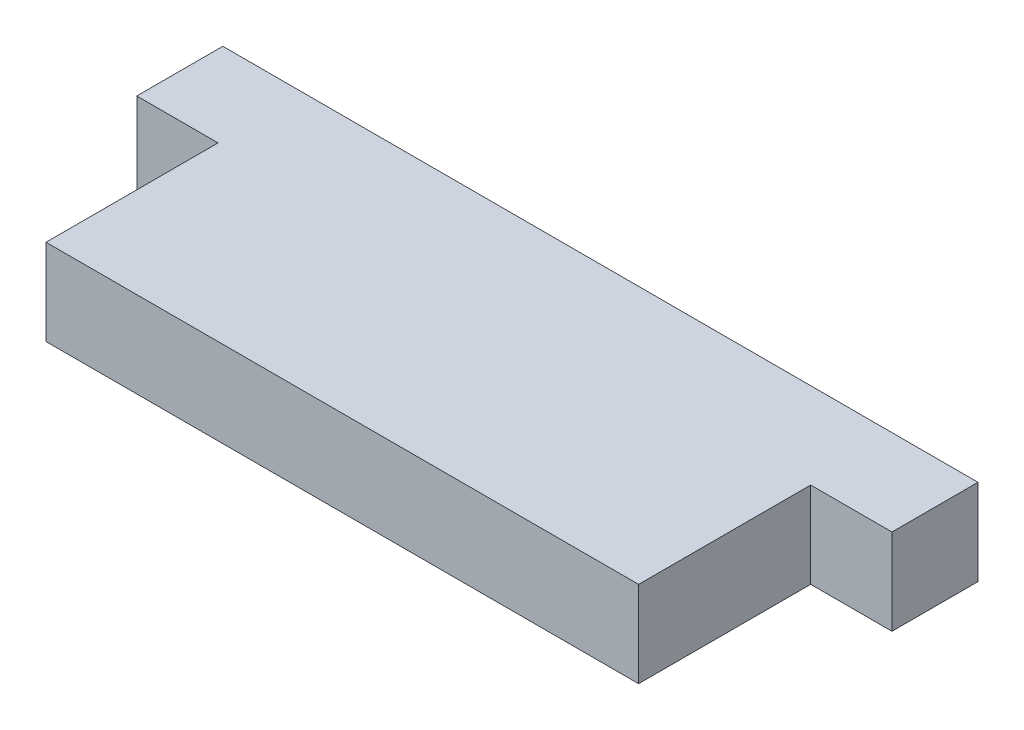
SolidWorks part; units mm, degrees
material "Beech"
ref_plane "Front Plane" through (0, 0, 0) normal (0, 0, 1) x (1, 0, 0)
ref_plane "Top Plane" through (0, 0, 0) normal (0, 1, 0) x (1, 0, 0)
ref_plane "Right Plane" through (0, 0, 0) normal (1, 0, 0) x (0, 0, -1)
sketch "Sketch1" plane through (0, 0, 0) normal (0, 1, 0) x (1, 0, 0)
  line L0 (0, 0) -> (0, 12.7)
  line L1 (0, 0) -> (43.74, 0)
  line L3 (43.74, 0) -> (43.74, 12.7)
  line L4 (-6.0001, 19.05) -> (49.7401, 19.05)
  line L5 (-6.0001, 19.05) -> (-6.0001, 12.7)
  line L6 (49.7401, 19.05) -> (49.7401, 12.7)
  line L7 (-6.0001, 12.7) -> (0, 12.7)
  line L8 (43.74, 12.7) -> (49.7401, 12.7)
  dimension "D1" = 12.7
  dimension "D2" = 43.74
  dimension "D3" = 6.35
  dimension "D4" = 6.0001
  dimension "D5" = 6.0001
extrude "Boss-Extrude1" add sketch "Sketch1" along normal blind 6.35
equation "\"MotorMountLegLength\"=.25in"
equation "\"GearOffset\"=.264907in"
equation "\"D4@Sketch1\"=\"TriggerRackOffset\""
equation "\"D5@Sketch1\"=\"TriggerRackOffset\""
equation "\"D2@Sketch1\" = \"CageLeftBottomEdge\" + \"CageRightBottomEdge\""
equation "\"CageLeftBottomEdge\"=22.11mm"
equation "\"CageLeftTopEdge\"=22.11mm"
equation "\"CageRightBottomEdge\"=21.63mm"
equation "\"CageRightTopEdge\"=21.63mm"
equation "\"CageHeight\"=86.04mm"
equation "\"CageLength\"=73.76mm"
equation "\"CageTopScrewClearance\"=10mm"
equation "\"CageBottomScrewClearance\"=25mm"
equation "\"CageLeftTopDepth\"= 11.65mm"
equation "\"CageLeftBottomDepth\"=11.11mm"
equation "\"CageLeftTopHeight\"=8.56175mm"
equation "\"CageLeftBottomHeight\"=16mm"
equation "\"CageRightTopDepth\"= 11.05mm"
equation "\"CageRightBottomDepth\"=10.58mm"
equation "\"CageRightTopHeight\"=9.6mm"
equation "\"CageRightBottomHeight\"=15.49mm"
equation "\"CageLeftTopChannelDepth\"=2.41908mm"
equation "\"CageLeftBottomChannelDepth\"=2.588mm"
equation "\"CageLeftChannelHeight\"=11.7mm"
equation "\"CageRightTopChannelDepth\"=2.32mm"
equation "\"CageRightBottomChannelDepth\"=2.318mm"
equation "\"CageRightChannelHeight\"=10mm"
equation "\"CageChanRelHeight\"=23.99mm"
equation "\"CageChanRelDepth\"=5.492mm"
equation "\"CageChamberRadius\"=16.261mm"
equation "\"CageScrewDiameter\"=4.8mm"
equation "\"CageSetScrewDiameter\"=3.5mm"
equation "\"CageAxleRadius\"=6.639mm"
equation "\"CageAxleKeyHeight\"=1.619mm"
equation "\"CageAxleKeyWidth\"=2.662mm"
equation "\"CageHoseWindowWidth\"=16.29mm"
equation "\"CageHoseWindowHeight\"=26.5mm"
equation "\"CageHoseWindow-Edge\"=8.89mm"
equation "\"CageScrew-VerticalEdge\"=5.0mm"
equation "\"CageScrew-HorizontalEdge\"=7.5mm"
equation "\"CageScrew-HoseCornerScrewEdge\"=4.45mm"
equation "\"CageAxle-BottomEdge\"=56.05mm"
equation "\"CageAxle-FrontEdge\"=46.03mm"
equation "\"CageBackSetScrew-Axle\"=40mm"
equation "\"CageFrontSetScrew-Axle\"=22mm"
equation "\"CageVelocityWindow-BackEdge\"=34.8mm"
equation "\"CageVelocityWindow-BottomEdge\"=27.55mm"
equation "\"CageVelocityWindowHeight\"=22.29mm"
equation "\"CageVelocityWindowWidth\"=12.61mm"
equation "\"TriggerSlot-BottomEdge\"=6.35mm"
equation "\"TriggerSlot-FrontEdge\"=15mm"
equation "\"TriggerSlotSize\"=6.7mm"
equation "\"TriggerRackOffset\"=.236224in"
equation "\"TriggerSlotSizeInt\"=.25in"
equation "\"TriggerSlotSpacing\"=.25in"
equation "\"TriggerMiniSlotWidth\"=3.5mm"
equation "\"TriggerRackWidth\"=6.5mm"
equation "\"whitemotordepth\"=11.27mm"
equation "\"whitemotorbackdepth\"=3.845mm"
equation "\"whitemotoraxledepth\" = 3.5mm"
equation "\"whitemotoraxleoffset\"=11.4mm"
equation "\"whitemotorwidth\"=12.07mm"
equation "\"whitemotorheight\"=16.68mm"
equation "\"whitemotorcylinderlength\" =13.04mm"
equation "\"whitemotorcylinderradius\"=3.845mm"
equation "\"whitemotorcylinderoffset\"=2.35mm"
equation "\"whitemotorcutoutlength\"=1.88mm"
equation "\"whitemotorouterrad\"=5mm"
equation "\"whitemotorinnerrad\"=2.95mm"
equation "\"elasticracklength\"=2in"
equation "\"elasticrackpegsize\"=.25in"
equation "\"elasticrackpegbuffer\"=.125in"
equation "\"elasticrackpegspacing\"=1.76476378in"
equation "\"elasticbaybuffer\"=.25in"
equation "\"elasticdepth\"=.125in"
equation "\"elasticbaydepth\"=.75in"
equation "\"motormountwidth\"=12mm"
equation "\"motormountcornerfillet\"=3mm"
equation "\"pandiscradius\"=14in"
equation "\"towermaterialwidth\"=.25in"
equation "\"towerslotlength\"=.5in"
equation "\"towermarkerspace\"=5in"
equation "\"towerslothorizoffset\"=1in"
equation "\"towerslothorizspacing\"=2in"
equation "\"towerslotvertoffset\"=3in"
equation "\"towerslotvertspacing\"=1in"
equation "\"towerheight\"=12in"
equation "\"towerupslot\"=1in"
equation "\"toweraxle\"=.5in"
equation "\"stepperouterrad\"=10mm"
equation "\"stepperscrewsize\"=3.45mm"
equation "\"stepperscrewc2c\"=49.5mm"
equation "\"stepperdepthoffset\"=24mm"
equation "\"stepperhorizoffset\"=22.91mm"
equation "\"shaftslotOD\"=18.8mm"
equation "\"shaftslotID\"=13.28mm"
equation "\"shaftkeywidth\"=2.67mm"
equation "\"shaftkeydepth\"=1.8mm"
equation "\"shaftcollartotaldepth\"=12.5mm"
equation "\"shaftsquaredepth\"=6mm"
equation "\"shaftsetscrewsize\"=3.5mm"
equation "\"shaftkeytightdepth\"=1.85mm"
equation "\"shaftslottightID\"=12.78mm"
equation "\"shaftsetscrewoffset\"=9mm"
equation "\"cagecollartotaldepth\"=10mm"
equation "\"cagecollartotalwidth\"=35mm"
equation "\"cagecollarbasedepth\"=4mm"
equation "\"gearhubintdiam\"=30mm"
equation "\"gearhubintwid\"=15mm"
equation "\"towerspeedwidth\"=2in"
equation "\"towerspeedheight\"=8in"
equation "\"towerspeedgap\"=2in"
equation "\"stepperaxleflat\"=.037in"
equation "\"stepperaxlerad\"=0.11811024in"
equation "\"ajaxaxlesize\"=3.87mm"
equation "\"ajaxinnercut\"=2.3mm"
equation "\"ajaxwidth\"=6.1mm"
equation "\"ajaxdiametral\"=25.8854"
equation "\"ajaxcutoutdepth\"=2.3mm"
equation "\"ajax4020gap\"=29.5mm"
equation "\"ajax4010gap\"=24.5mm"
equation "\"ajax20hubbuffer\"=0.240157in"
equation "\"ajax20hubholeoffset\"=.19685in"
equation "\"ajax20hubholesize\"=.059055in"
equation "\"ajax20cutoutint\"=13.4mm"
equation "\"ajax40hubholesize\"=7.21mm"
equation "\"ajax40hubholeoffset\"=10mm"
equation "\"ajax40hubbuffer\"=.350394in"
equation "\"ajax40cutoutint\"=32.6mm"
equation "\"bearingpandiscrad\"=6.8in"
equation "\"bearingpandiscang\"=48.75deg"
equation "\"bearingclearholedist\"=4.7345in"
equation "\"bearingclearholesize\"=.5in"
equation "\"bearingclearholeang\"=22.5deg"
equation "\"bearingmountholedist\"=4.25in"
equation "\"bearingwirehole\"=1.5in"
equation "\"no6diam\"=.146in"
equation "\"shortconangle\"=20deg"
equation "\"shortconlen\"=.875in"
equation "\"longconlen\"=1.25in"
equation "\"longconangle\"=15deg"
equation "\"TGMGearFaceDiameter\"=24.40mm"
equation "\"TGMCylinderLength\"=15.00mm"
equation "\"TGMScrewHole-Center\"=8.70mm"
equation "\"TGMScrewHoleDiameter\"=5.04mm"
equation "\"TGMCenterHoleDiameter\"=9.50mm"
equation "\"TGMShaftCollarSideLength\"=19.00mm"
equation "\"TGMShaftCollarDockingDepth\"=7.00mm"
equation "\"towerplatslotoffset\"=1.5in"
equation "\"towermotorpanelheight\"=10in"
equation "\"towerplatdepth\"=2in"
equation "\"ajaxhubdepth\"=.25in"
equation "\"shconangle\"=20deg"
equation "\"shconlen\"=1in"
equation "\"lnconlen\"=1.5in"
equation "\"lnconangle\"=15deg"
